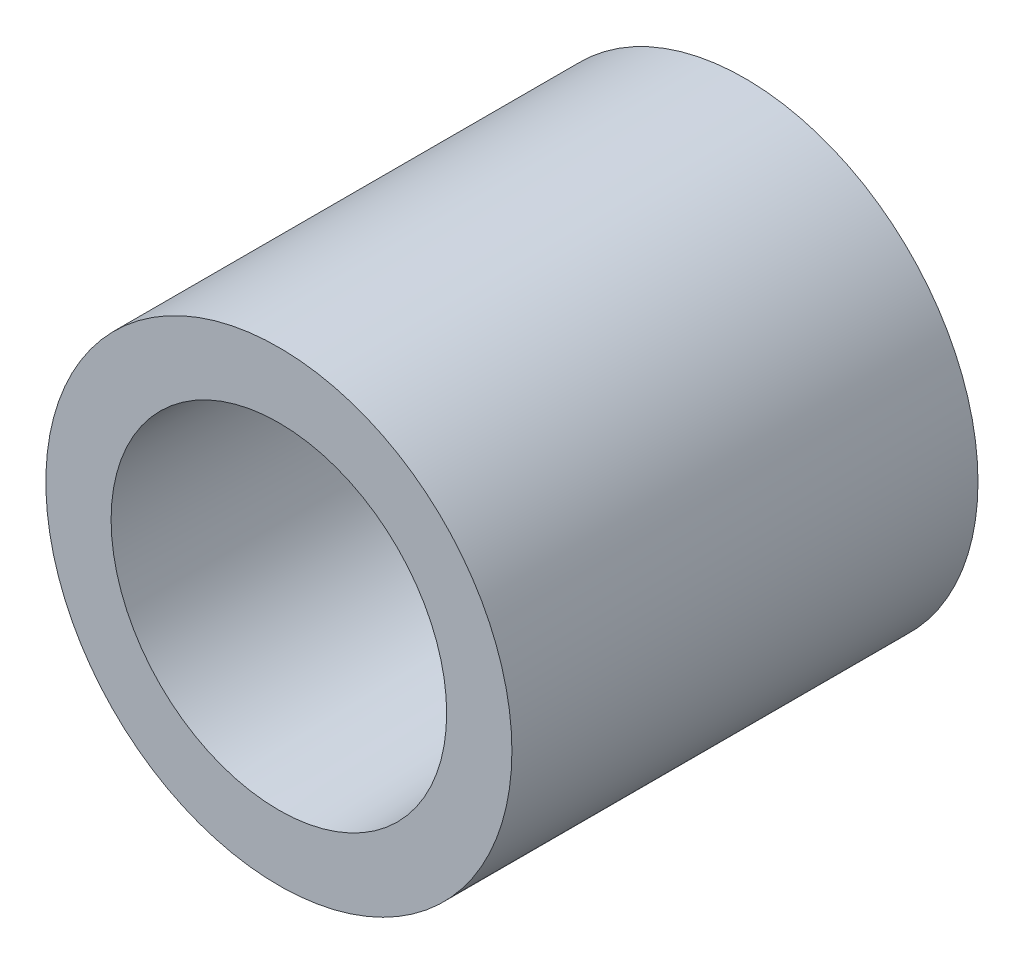
SolidWorks part; units mm, degrees
material "6061 Alloy"
ref_plane "Front Plane" through (0, 0, 0) normal (0, 0, 1) x (1, 0, 0)
ref_plane "Top Plane" through (0, 0, 0) normal (0, 1, 0) x (1, 0, 0)
ref_plane "Right Plane" through (0, 0, 0) normal (1, 0, 0) x (0, 0, -1)
sketch "Sketch1" plane through (0, 0, 0) normal (0, 0, 1) x (1, 0, 0)
  circle A0 centre (0, 0) radius 9.525
  dimension "D1" = 19.05
extrude "Boss-Extrude1" add sketch "Sketch1" along normal blind 19.05
sketch "Sketch2" plane through (0, 0, 19.05) normal (0, 0, 1) x (1, 0, 0)
  circle A0 centre (0, 0) radius 25.7291
hole_wizard "1/4 NPT Tapped Hole1" positions "Sketch5" profile "Sketch6" size "1/4" standard "ANSI Inch"
sketch "Sketch5" plane through (0, 0, 19.05) normal (0, 0, 1) x (1, 0, 0)
  point P0 (0, 0)
sketch "Sketch6" plane through (0, 0, 19.05) normal (1, 0, 0) x (0, -1, 0)
  line L0 (0, 0) -> (0, 14.7723)
  line L1 (5.5626, 11.43) -> (0, 14.7723)
  line L2 (-5.5626, 11.43) -> (0, 14.7723) construction
  line L3 (5.5626, 11.43) -> (5.5626, 10.0203)
  line L4 (5.5626, 10.0203) -> (6.558, 10.0203)
  line L5 (6.558, 10.0203) -> (6.858, 0)
  line L6 (-6.558, 10.0203) -> (-6.858, 0) construction
  line L7 (6.858, 0) -> (0, 0)
  line L8 (0, -6.35) -> (0, 107.95) construction
  line L11 (-5.5626, 10.0203) -> (-6.558, 10.0203) construction
  dimension "Tap Drill Dia." = 11.1252
  dimension "Tap Drill Depth" = 11.43
  dimension "Thread Dia." = 13.716
  dimension "Thread Angle" = 3.43
  dimension "Thread Depth" = 10.0203
  dimension "Drill Angle" = 118
sketch "Sketch7" plane through (0, 0, 0) normal (0, 0, -1) x (-1, 0, 0)
  circle A0 centre (0, 0) radius 0.9218
hole_wizard "CBORE for 1/4 Socket Head Cap Screw1" positions "Sketch8" profile "Sketch9" counterbore size "1/4" standard "ANSI Inch"
sketch "Sketch8" plane through (0, 0, 0) normal (0, 0, -1) x (-1, 0, 0)
  point P0 (0, 0)
sketch "Sketch9" plane through (0, 0, 0) normal (1, 0, 0) x (0, 1, 0)
  line L0 (0, 0) -> (0, 12.9385)
  line L1 (0, 12.9385) -> (0.3969, 12.7)
  line L2 (0.3969, 12.7) -> (0.3969, 3.175)
  line L3 (0.3969, 3.175) -> (1.5875, 3.175)
  line L4 (1.5875, 3.175) -> (1.5875, 0)
  line L5 (1.5875, 0) -> (0, 0)
  line L10 (0, 12.9385) -> (-0.3969, 12.7) construction
  line L11 (0, -6.35) -> (0, 107.95) construction
  dimension "Hole Dia." = 0.7937
  dimension "Hole Depth" = 12.7
  dimension "C'Bore Dia." = 3.175
  dimension "C'Bore Depth" = 3.175
  dimension "Drill Angle" = 118
